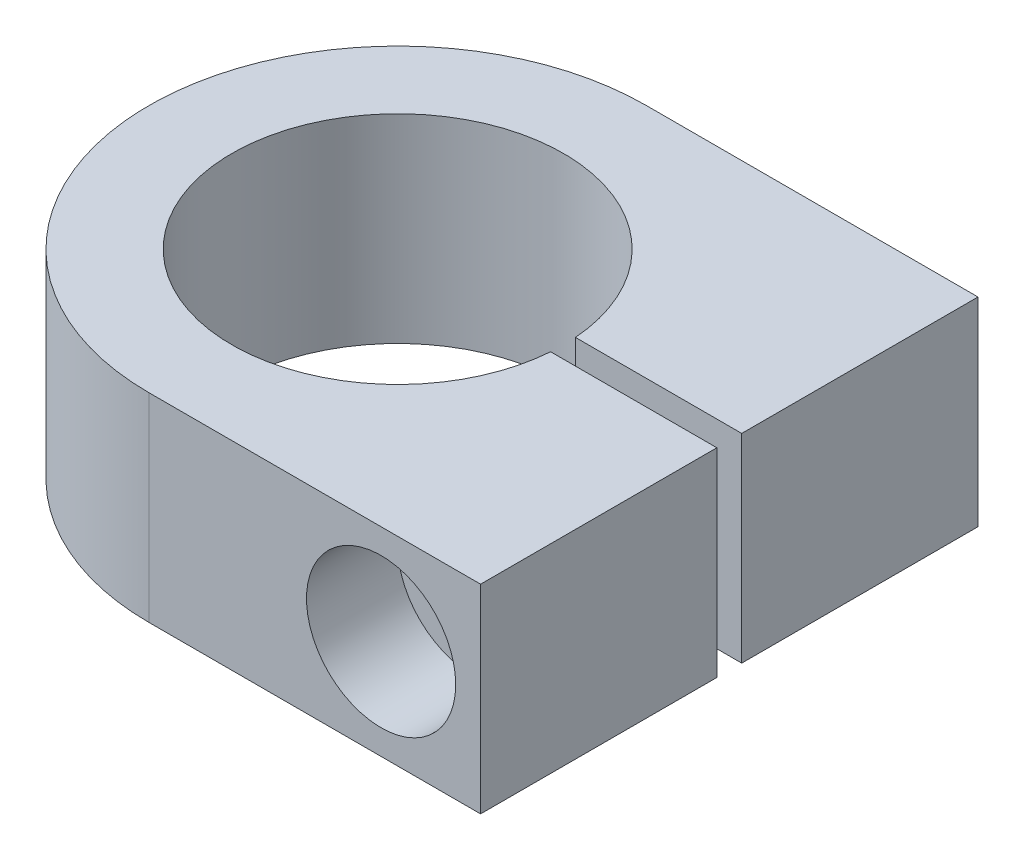
SolidWorks part; units mm, degrees
ref_plane "Přední rovina" through (0, 0, 0) normal (0, 0, 1) x (1, 0, 0)
ref_plane "Vrchní rovina" through (0, 0, 0) normal (0, 1, 0) x (1, 0, 0)
ref_plane "Pravá rovina" through (0, 0, 0) normal (1, 0, 0) x (0, 0, -1)
sketch "Skica1" plane through (0, 0, 0) normal (0, 1, 0) x (1, 0, 0)
  line L0 (0, 0) -> (0, 28.5)
  line L1 (0, 28.5) -> (-20.0563, 28.5)
  line L2 (-20.0563, 31.5) -> (0, 31.5)
  line L3 (0, 31.5) -> (0, 60)
  line L4 (0, 60) -> (-40, 60)
  line L5 (-40, 0) -> (0, 0)
  arc A1 (-40, 60) -> (-40, 0) centre (-40, 30) ccw
  arc A3 (-20.0563, 31.5) -> (-20.0563, 28.5) centre (-40, 30) ccw
  point P3 (0, 0)
  point P10 (0, 0)
  dimension "D2" = 70
  dimension "D4" = 20
  dimension "D1" = 60
  dimension "D3" = 3
extrude "Přidat vysunutím1" add sketch "Skica1" along normal blind 24
sketch "Skica2" plane through (0, 0, 0) normal (0, 0, 1) x (1, 0, 0)
  line L0 (-40, 0) -> (0, 0) construction
  line L1 (-40, 24) -> (-40, 0) construction
  circle A0 centre (-12, 12) radius 5.5
  dimension "D1" = 11
  dimension "D2" = 12
  dimension "D3" = 28
extrude "Odebrat vysunutím1" cut sketch "Skica2" against normal up to next contours A0
sketch "Skica3" plane through (0, 0, 0) normal (0, 0, 1) x (1, 0, 0)
  circle A0 centre (-12, 12) radius 9
  dimension "D1" = 18
extrude "Odebrat vysunutím2" cut sketch "Skica3" against normal blind 11
sketch "Skica4" plane through (0, 0, -60) normal (0, 0, -1) x (-1, 0, 0)
  line L0 (0, 12) -> (40, 12) construction
  line L1 (0, 24) -> (0, 0) construction
  line L2 (40, 24) -> (40, 0) construction
  line L3 (12, 33.2657) -> (12, -7.8239) construction
  point P8 (12, 12)
  dimension "D1" = 28
hole_wizard "M10 závit1" positions "Skica5" profile "Skica6" tap size "M10" standard "ISO" end condition up to next
sketch "Skica5" plane through (0, 0, -60) normal (0, 0, -1) x (-1, 0, 0)
  point P0 (12, 12)
sketch "Skica6" plane through (-12, 12, -60) normal (1, 0, 0) x (0, 1, 0)
  line L0 (0, 0) -> (0, 28.5)
  line L1 (0, 28.5) -> (4.25, 28.5)
  line L2 (4.25, 28.5) -> (4.25, 0)
  line L5 (4.25, 0) -> (0, 0)
  line L11 (0, -6.35) -> (0, 107.95) construction
  dimension "Průměr závitníku" = 8.5
  dimension "Hloubka závitníku" = 28.5
cosmetic thread "Závit díry1" parameters "D2"=10
